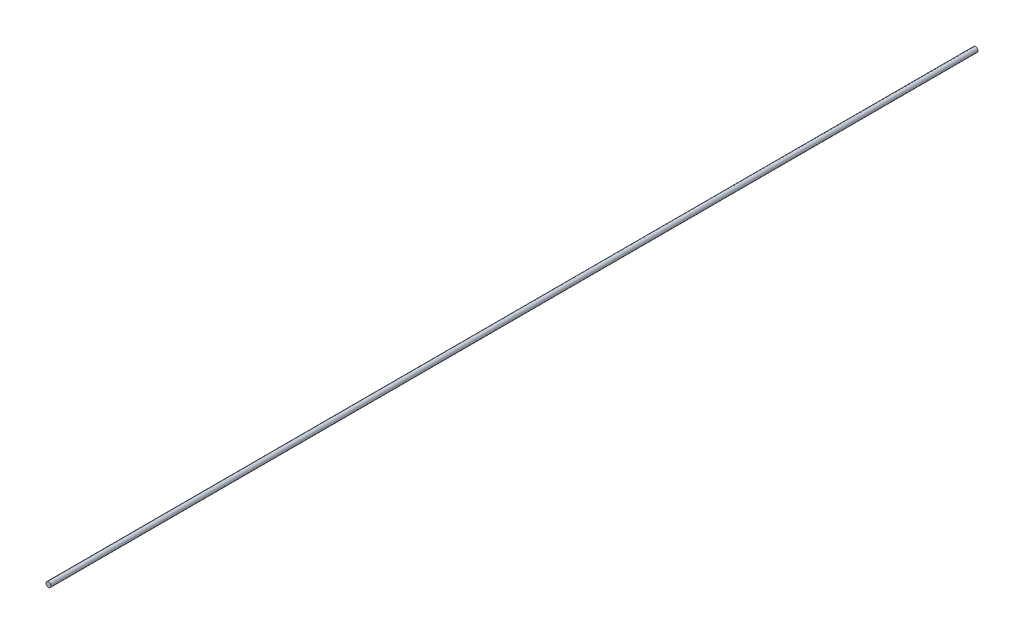
SolidWorks part; units mm, degrees
ref_plane "Front Plane" through (0, 0, 0) normal (0, 0, 1) x (1, 0, 0)
ref_plane "Top Plane" through (0, 0, 0) normal (0, 1, 0) x (1, 0, 0)
ref_plane "Right Plane" through (0, 0, 0) normal (1, 0, 0) x (0, 0, -1)
sketch "Sketch1" plane through (0, 0, 0) normal (0, 0, 1) x (1, 0, 0)
  circle A0 centre (0, 0) radius 1.8161
  dimension "D1" = 3.6322
extrude "Boss-Extrude1" add sketch "Sketch1" along normal blind 685.8
